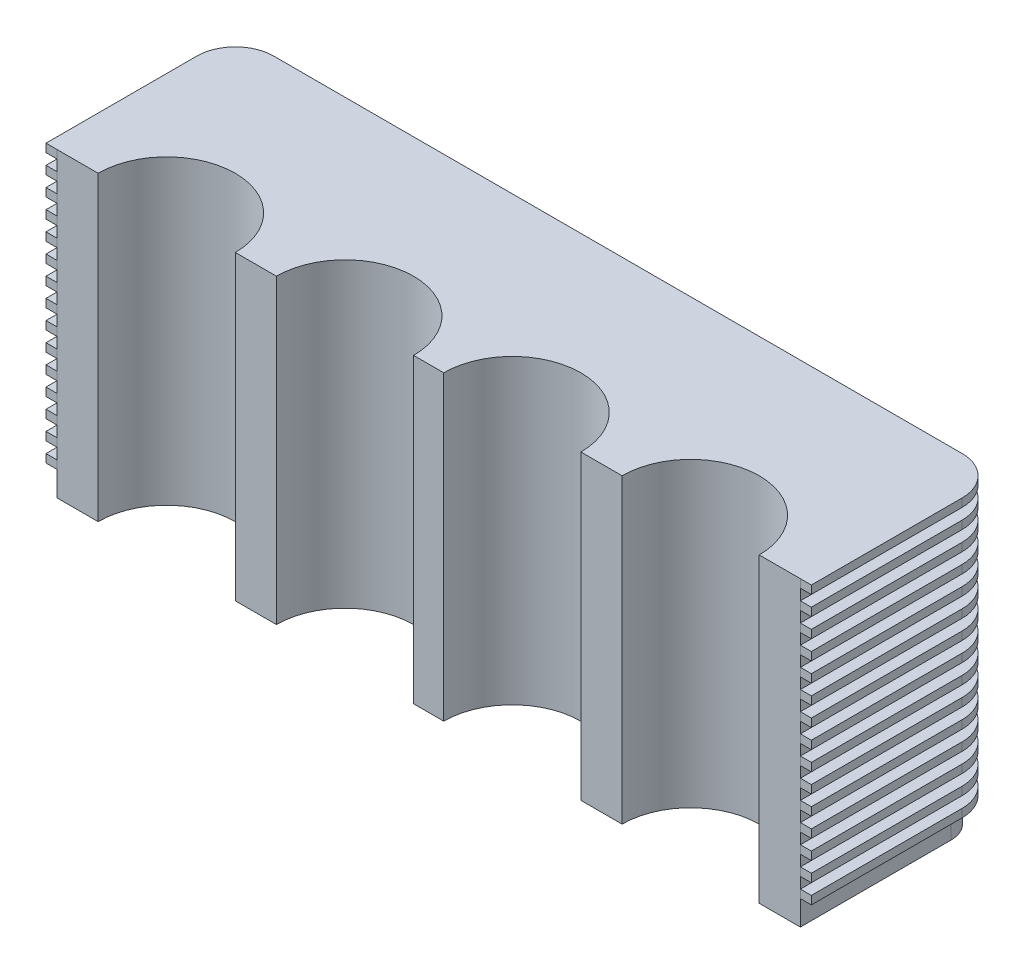
SolidWorks part; units mm, degrees
ref_plane "Front Plane" through (0, 0, 0) normal (0, 0, 1) x (1, 0, 0)
ref_plane "Top Plane" through (0, 0, 0) normal (0, 1, 0) x (1, 0, 0)
ref_plane "Right Plane" through (0, 0, 0) normal (1, 0, 0) x (0, 0, -1)
sketch "Sketch1" plane through (0, 0, 0) normal (0, 1, 0) x (1, 0, 0)
  line L0 (0, 1651) -> (6883.4, 0) construction
  line L1 (0, 0) -> (381, 0)
  line L2 (0, 0) -> (0, 1397)
  line L3 (254, 1651) -> (6629.4, 1651)
  line L4 (6883.4, 0) -> (6883.4, 1397)
  line L5 (6883.4, 1651) -> (1533.6088, 367.8398) construction
  line L6 (3441.7, 1651) -> (3441.7, 0) construction
  line L7 (4851.4, 0) -> (5232.4, 0)
  line L8 (6502.4, 0) -> (6883.4, 0)
  line L9 (1651, 0) -> (2032, 0)
  line L10 (387.8512, 93.027) -> (0, 0) construction
  line L11 (3302, 0) -> (3581.4, 0)
  arc A0 (6629.4, 1651) -> (6883.4, 1397) centre (6629.4, 1397) cw
  arc A1 (0, 1397) -> (254, 1651) centre (254, 1397) cw
  arc A2 (6502.4, 0) -> (5232.4, 0) centre (5867.4, 0) ccw
  arc A3 (4851.4, 0) -> (3581.4, 0) centre (4216.4, 0) ccw
  arc A4 (381, 0) -> (1651, 0) centre (1016, 0) cw
  arc A5 (2032, 0) -> (3302, 0) centre (2667, 0) cw
  dimension "D1" = 254
  dimension "D4" = 1270
  dimension "D5" = 635
  dimension "D2" = 1651
  dimension "D3" = 6883.4
  dimension "D6" = 381
  dimension "D7" = 381
extrude "Boss-Extrude1" add sketch "Sketch1" along normal blind 2794
sketch "Sketch5" plane through (0, 2794, 0) normal (0, 1, 0) x (1, 0, 0)
  line L1 (6985, 0.1246) -> (6985, 1397)
  line L2 (6629.4, 1752.6) -> (254, 1752.6)
  line L3 (-101.6, 1397) -> (-101.6, 0.0461)
  line L4 (6883.4, 0.1246) -> (6985, 0.1246)
  line L5 (0, 0.0461) -> (-101.6, 0.0461)
  line L8 (0, 1397) -> (0, 0)
  line L9 (0, 0) -> (381, 0)
  line L10 (1651, 0) -> (2032, 0)
  line L11 (3302, 0) -> (3581.4, 0)
  line L12 (4851.4, 0) -> (5232.4, 0)
  line L13 (6502.4, 0) -> (6883.4, 0)
  line L14 (6883.4, 0) -> (6883.4, 1397)
  line L15 (6629.4, 1651) -> (254, 1651)
  line L16 (0, 1397) -> (0, 0.0461)
  line L22 (6883.4, 0.1246) -> (6883.4, 1397)
  line L23 (6629.4, 1651) -> (254, 1651)
  arc A0 (6985, 1397) -> (6629.4, 1752.6) centre (6629.4, 1397) ccw
  arc A1 (254, 1752.6) -> (-101.6, 1397) centre (254, 1397) ccw
  arc A6 (1651, 0) -> (381, 0) centre (1016, 0) ccw
  arc A7 (3302, 0) -> (2032, 0) centre (2667, 0) ccw
  arc A8 (4851.4, 0) -> (3581.4, 0) centre (4216.4, 0) ccw
  arc A9 (6502.4, 0) -> (5232.4, 0) centre (5867.4, 0) ccw
  arc A10 (6883.4, 1397) -> (6629.4, 1651) centre (6629.4, 1397) ccw
  arc A11 (254, 1651) -> (0, 1397) centre (254, 1397) ccw
  arc A16 (6883.4, 1397) -> (6629.4, 1651) centre (6629.4, 1397) ccw
  arc A17 (254, 1651) -> (0, 1397) centre (254, 1397) ccw
  dimension "D1" = 0
  dimension "D2" = 101.6
extrude "Boss-Extrude4" add sketch "Sketch5" against normal blind 76.2
pattern_linear "LPattern1" count 15 spacing 177.8 along (0, -1, 0) of "Boss-Extrude4"
